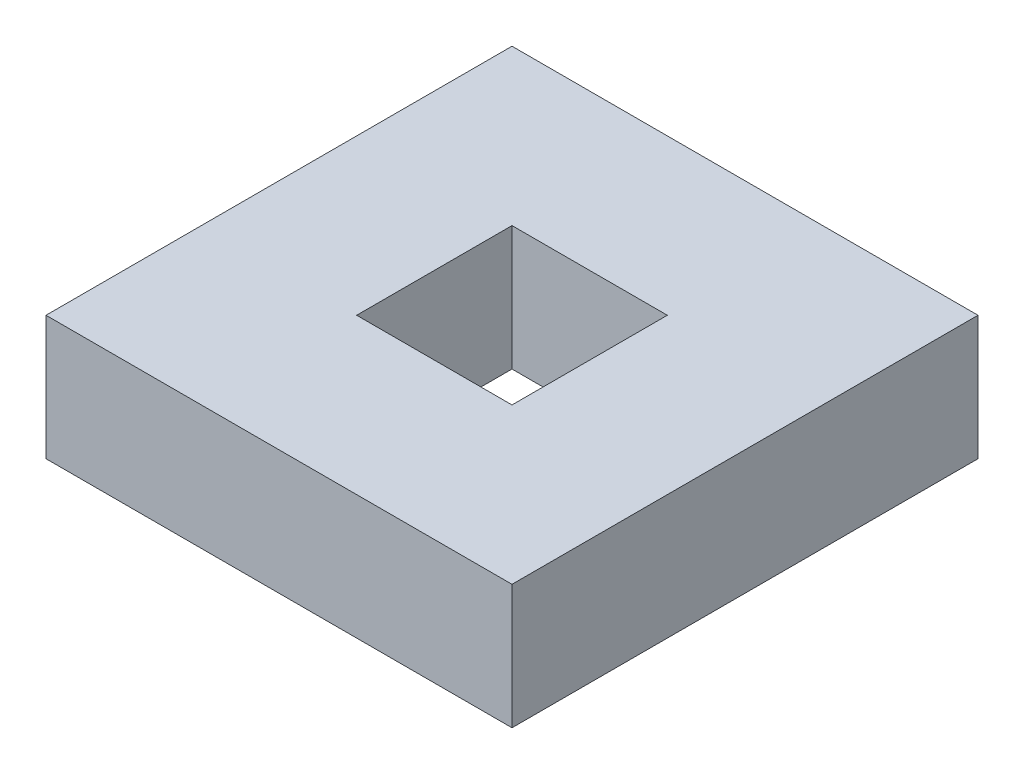
SolidWorks part; units mm, degrees
ref_plane "Front Plane" through (0, 0, 0) normal (0, 0, 1) x (1, 0, 0)
ref_plane "Top Plane" through (0, 0, 0) normal (0, 1, 0) x (1, 0, 0)
ref_plane "Right Plane" through (0, 0, 0) normal (1, 0, 0) x (0, 0, -1)
sketch "Sketch1" plane through (0, 0, 0) normal (0, 1, 0) x (1, 0, 0)
  line L1 (0, 3) -> (3, 3)
  line L2 (0, 3) -> (0, 0)
  line L3 (0, 0) -> (3, 0)
  line L4 (3, 3) -> (3, 0)
  point P4 (0, 0)
  dimension "D1" = 3
  dimension "D2" = 3
extrude "Boss-Extrude1" add sketch "Sketch1" along normal blind 0.8
sketch "Sketch2" plane through (0, 0.8, 0) normal (0, 1, 0) x (1, 0, 0)
  line L0 (0, 0) -> (3, 0) construction
  line L1 (1, 2) -> (2, 2)
  line L2 (1, 2) -> (1, 1)
  line L3 (1, 1) -> (2, 1)
  line L4 (2, 2) -> (2, 1)
  line L5 (3, 0) -> (3, 3) construction
  point P6 (1.5, 0)
  point P7 (1.5, 1)
  point P10 (3, 1.5)
  point P11 (2, 1.5)
  dimension "D1" = 1
  dimension "D2" = 1
extrude "Cut-Extrude1" cut sketch "Sketch2" against normal blind 1.6
